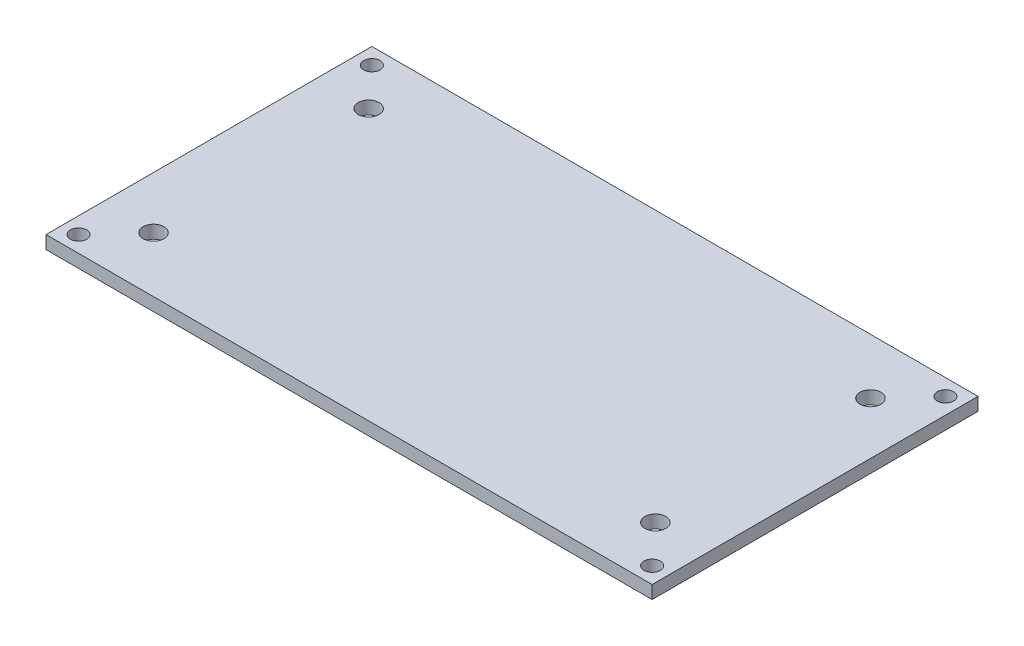
SolidWorks part; units mm, degrees
ref_plane "Front Plane" through (0, 0, 0) normal (0, 0, 1) x (1, 0, 0)
ref_plane "Top Plane" through (0, 0, 0) normal (0, 1, 0) x (1, 0, 0)
ref_plane "Right Plane" through (0, 0, 0) normal (1, 0, 0) x (0, 0, -1)
sketch "Sketch1" plane through (0, 0, 0) normal (0, 1, 0) x (1, 0, 0)
  line L1 (-46.5, 25) -> (46.5, 25)
  line L2 (-46.5, 25) -> (-46.5, -25)
  line L3 (-46.5, -25) -> (46.5, -25)
  line L4 (46.5, 25) -> (46.5, -25)
  line L5 (-46.5, 25) -> (46.5, -25) construction
  line L6 (-46.5, -25) -> (46.5, 25) construction
  point P0 (0, 0)
  dimension "D1" = 50
  dimension "D2" = 93
extrude "Boss-Extrude1" add sketch "Sketch1" along normal blind 2
sketch "Sketch2" plane through (0, 2, 0) normal (0, 1, 0) x (1, 0, 0)
  line L0 (-46.5, 25) -> (-46.5, -25) construction
  line L1 (-46.5, -25) -> (46.5, -25) construction
  line L2 (46.5, 25) -> (-46.5, 25) construction
  line L3 (46.5, -25) -> (46.5, 25) construction
  circle A0 centre (-44, 22.5) radius 1.25
  circle A1 centre (44, 22.5) radius 1.25
  circle A2 centre (44, -22.5) radius 1.25
  circle A3 centre (-44, -22.5) radius 1.25
  point P16 (46.2486, 22.3163)
  point P19 (40.9846, 22.3163)
  dimension "D1" = 2.5
  dimension "D2" = 2.5
  dimension "D3" = 2.5
  dimension "D4" = 2.5
  dimension "D5" = 2.5
  dimension "D6" = 2.5
  dimension "D7" = 2.5
  dimension "D8" = 2.5
  dimension "D9" = 2.5
  dimension "D10" = 2.5
  dimension "D11" = 2.5
  dimension "D12" = 2.5
extrude "Cut-Extrude1" cut sketch "Sketch2" against normal blind 2
sketch "Sketch3" plane through (0, 2, 0) normal (0, 1, 0) x (1, 0, 0)
  line L0 (-46.5, 0) -> (46.5, 0) construction
  line L1 (-46.5, 25) -> (-46.5, -25) construction
  line L2 (46.5, -25) -> (46.5, 25) construction
  line L3 (0, 25) -> (0, -25) construction
  line L4 (46.5, 25) -> (-46.5, 25) construction
  line L5 (-46.5, -25) -> (46.5, -25) construction
  circle A0 centre (-38.5, 16.5) radius 1.6
  circle A1 centre (-38.5, -16.5) radius 1.6
  circle A2 centre (38.5, 16.5) radius 1.6
  circle A3 centre (38.5, -16.5) radius 1.6
  point P20 (0, 0)
  point P21 (0, 0)
  dimension "D3" = 3.2
  dimension "D4" = 3.2
  dimension "D8" = 3.2
  dimension "D9" = 3.2
  dimension "D1" = 33
  dimension "D2" = 16.5
  dimension "D5" = 77
  dimension "D6" = 33
  dimension "D7" = 16.5
  dimension "D10" = 77
  dimension "D11" = 38.5
  dimension "D12" = 38.5
extrude "Cut-Extrude2" cut sketch "Sketch3" against normal blind 2
